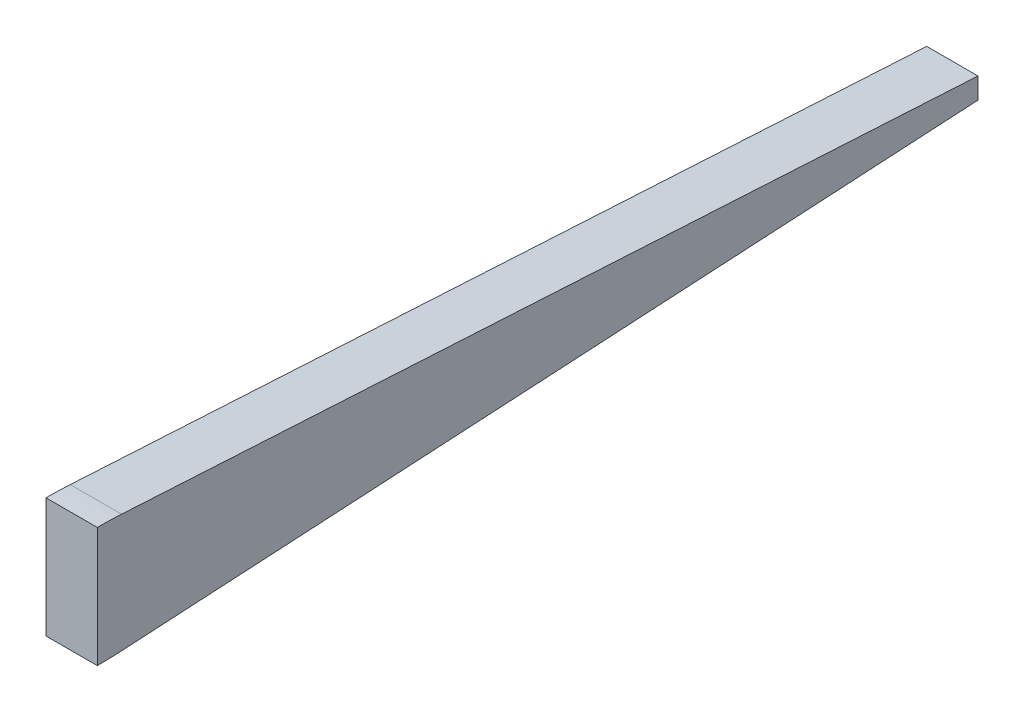
SolidWorks part; units mm, degrees
material "Cedar"
ref_plane "Front" through (0, 0, 0) normal (0, 0, 1) x (1, 0, 0)
ref_plane "Top" through (0, 0, 0) normal (0, 1, 0) x (1, 0, 0)
ref_plane "Right" through (0, 0, 0) normal (1, 0, 0) x (0, 0, -1)
sketch "Sketch1" plane through (0, 0, 0) normal (1, 0, 0) x (0, 0, -1)
  line L0 (55, 14) -> (100, 14) construction
  line L1 (105.6773, 13.8387) -> (302.1523, 2.6661)
  line L2 (308, 2.5) -> (348.8038, 2.5) construction
  line L3 (0, 0) -> (348.8038, 0) construction
  line L4 (302.1523, 2.6661) -> (306, 2.4473)
  line L5 (55, 14) -> (55, 17) construction
  line L6 (55, 17) -> (100, 17) construction
  line L7 (105.8477, 16.8339) -> (302.3227, 5.6613) construction
  line L8 (308, 5.5) -> (339.4737, 5.5) construction
  line L9 (348.8038, 2.5) -> (348.8038, 3) construction
  line L10 (348.8038, 3) -> (339.4737, 5.5) construction
  line L11 (348.8038, 0) -> (360, 0) construction
  line L12 (360, 0) -> (348.8038, 3) construction
  line L13 (306, 2.4473) -> (306, 0)
  line L14 (306, 0) -> (100, 0)
  line L16 (100, 14) -> (100, 0)
  arc A0 (100, 14) -> (105.6773, 13.8387) centre (100, -86) cw
  arc A1 (302.1523, 2.6661) -> (308, 2.5) centre (308, 105.5) ccw construction
  arc A2 (100, 17) -> (105.8477, 16.8339) centre (100, -86) cw construction
  arc A3 (302.3227, 5.6613) -> (308, 5.5) centre (308, 105.5) ccw construction
  dimension "D5" = 100
  dimension "D6" = 100
  dimension "D1" = 2.5
  dimension "D2" = 45
  dimension "D3" = 14
  dimension "D4" = 52
  dimension "D7" = 3
  dimension "D8" = 0.5
  dimension "D9" = 15
  dimension "D10" = 360
  dimension "D11" = 55
  dimension "D12" = 2
extrude "Extrude1" add sketch "Sketch1" along normal mid plane 12
mirror "Mirror1" about plane through (6, 0, -306) normal (0, 1, 0) of "Extrude1"
